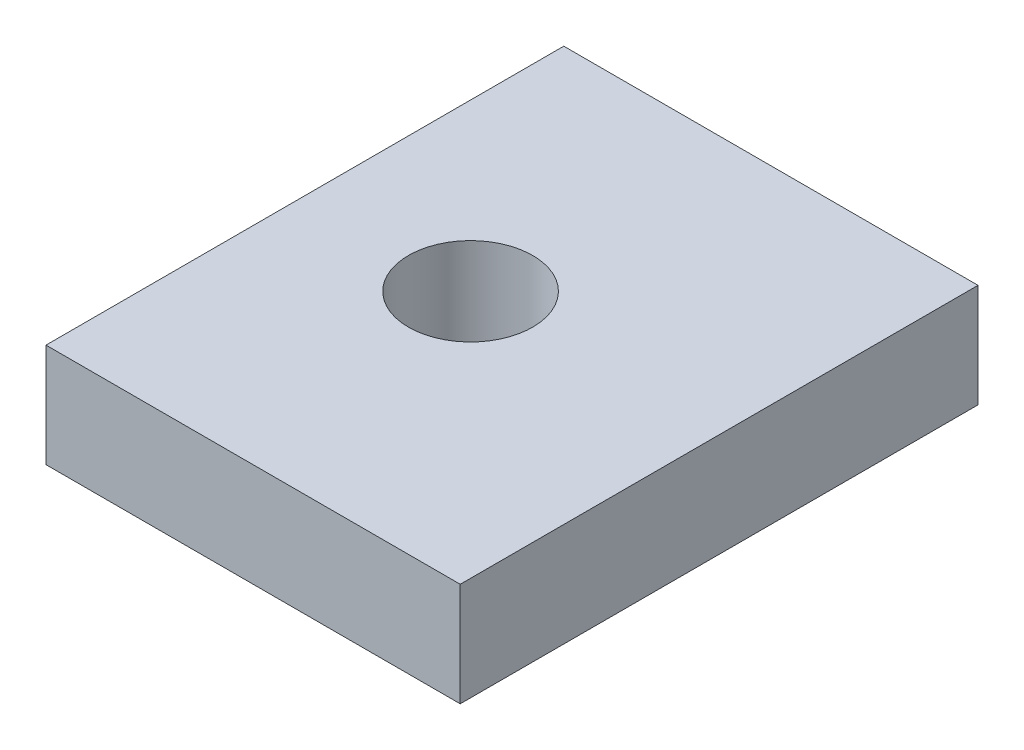
SolidWorks part; units mm, degrees
ref_plane "Plan de face" through (0, 0, 0) normal (0, 0, 1) x (1, 0, 0)
ref_plane "Plan de dessus" through (0, 0, 0) normal (0, 1, 0) x (1, 0, 0)
ref_plane "Plan de droite" through (0, 0, 0) normal (1, 0, 0) x (0, 0, -1)
sketch "Esquisse1" plane through (0, 0, 0) normal (0, 0, 1) x (1, 0, 0)
  line L1 (0, 0) -> (20, 0)
  line L2 (0, 0) -> (0, -5)
  line L3 (0, -5) -> (20, -5)
  line L4 (20, 0) -> (20, -5)
  dimension "D1" = 20
  dimension "D2" = 5
extrude "Boss.-Extru.1" add sketch "Esquisse1" along normal blind 25
sketch "Esquisse2" plane through (0, 0, 0) normal (0, 1, 0) x (1, 0, 0)
  line L0 (20, 0) -> (0, 0) construction
  line L1 (0, -25) -> (0, 0) construction
  circle A0 centre (8, -12.5) radius 3
  point P4 (0, 0)
  point P6 (33.2116, -57.2569)
  dimension "D1" = 6
  dimension "D2" = 12.5
  dimension "D3" = 8
extrude "Enlèv. mat.-Extru.1" cut sketch "Esquisse2" against normal through all
